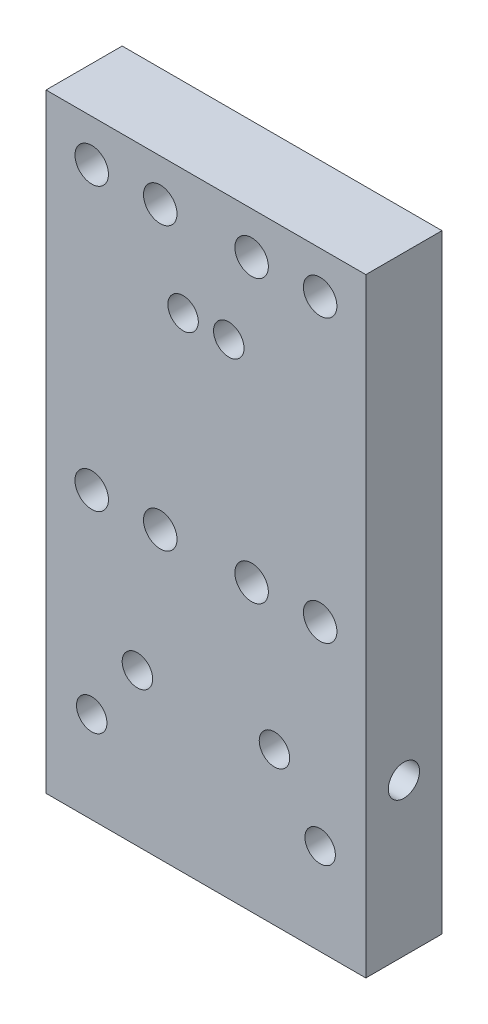
SolidWorks part; units mm, degrees
material "Ceramic Porcelain"
ref_plane "Front Plane" through (0, 0, 0) normal (0, 0, 1) x (1, 0, 0)
ref_plane "Top Plane" through (0, 0, 0) normal (0, 1, 0) x (1, 0, 0)
ref_plane "Right Plane" through (0, 0, 0) normal (1, 0, 0) x (0, 0, -1)
sketch "Sketch1" plane through (0, 0, 0) normal (0, 1, 0) x (1, 0, 0)
  line L1 (-10.5, 2.5) -> (10.5, 2.5)
  line L2 (-10.5, 2.5) -> (-10.5, -2.5)
  line L3 (-10.5, -2.5) -> (10.5, -2.5)
  line L4 (10.5, 2.5) -> (10.5, -2.5)
  point P4 (0, 2.5)
  point P6 (10.5, 0)
  dimension "D1" = 21
  dimension "D2" = 5
extrude "Boss-Extrude1" add sketch "Sketch1" along normal blind 40
hole_wizard "M2.5 Tapped Hole1" positions "Sketch4" profile "Sketch5" tap size "M2.5" standard "ISO"
sketch "Sketch4" plane through (0, 0, 0) normal (0, -1, 0) x (-1, 0, 0)
  line L0 (-10.5, 2.5) -> (10.5, 2.5) construction
  line L1 (-10.5, -2.5) -> (-10.5, 2.5) construction
  line L2 (-10.5, 2.5) -> (10.5, 2.5)
  line L3 (-10.5, -2.5) -> (-10.5, 2.5)
  line L4 (10.5, 2.5) -> (10.5, -2.5) construction
  point P0 (7.5, 0)
  point P2 (-7.5, 0)
  point P9 (-10.5, 0)
  dimension "D1" = 3
  dimension "D2" = 3
cosmetic thread "Hole Thread1" parameters "D1"=5, "D2"=2.5
cosmetic thread "Hole Thread2" parameters "D1"=5, "D2"=2.5
sketch "Sketch5" plane through (-7.5, 0, 0) normal (1, 0, 0) x (0, 0, -1)
  line L0 (0, 0) -> (0, 10.6159)
  line L1 (0, 10.6159) -> (1.025, 10)
  line L2 (1.025, 10) -> (1.025, 0)
  line L5 (1.025, 0) -> (0, 0)
  line L10 (0, 10.6159) -> (-1.025, 10) construction
  line L11 (0, -6.35) -> (0, 107.95) construction
  dimension "Tap Drill Dia." = 2.05
  dimension "Tap Drill Depth" = 10
  dimension "Drill Angle" = 118
hole_wizard "M2 Clearance Hole1" positions "Sketch6" profile "Sketch7" hole size "M2" standard "ISO" end condition through all
sketch "Sketch6" plane through (0, 0, -2.5) normal (0, 0, -1) x (-1, 0, 0)
  line L0 (10.5, 40) -> (10.5, 0) construction
  line L1 (-10.5, 40) -> (-10.5, 0) construction
  line L2 (-10.5, 40) -> (10.5, 40) construction
  line L3 (10.5, 40) -> (10.5, 0)
  line L4 (-10.5, 40) -> (-10.5, 0)
  line L5 (-10.5, 40) -> (10.5, 40)
  line L11 (-10.5, 17) -> (10.5, 17)
  line L13 (-10.5, 35.5) -> (10.5, 35.5)
  point P0 (-7.5, 37.25)
  point P2 (7.5, 37.25)
  point P4 (-7.5, 18.75)
  point P6 (7.5, 18.75)
  point P30 (-3, 37.25)
  point P32 (3, 37.25)
  point P35 (-3, 18.75)
  point P37 (3, 18.75)
  dimension "D1" = 3
  dimension "D2" = 3
  dimension "D3" = 4.5
  dimension "D4" = 23
  dimension "D5" = 1.75
  dimension "D6" = 1.75
  dimension "D7" = 4.5
  dimension "D8" = 4.5
sketch "Sketch7" plane through (7.5, 37.25, -2.5) normal (1, 0, 0) x (0, 1, 0)
  line L0 (0, 0) -> (0, 5)
  line L1 (0, 5) -> (1.1, 5)
  line L2 (1.1, 5) -> (1.1, 0)
  line L5 (1.1, 0) -> (0, 0)
  line L11 (0, -6.35) -> (0, 107.95) construction
  dimension "Thru Hole Dia." = 2.2
  dimension "Thru Hole Depth" = 5
hole_wizard "Ø2.0 (2) Diameter Hole2" positions "Sketch8" profile "Sketch9" hole size "Ø2.0" standard "ISO" end condition through all
sketch "Sketch8" plane through (0, 0, -2.5) normal (0, 0, -1) x (-1, 0, 0)
  line L9 (-1.5, 31.81) -> (1.5, 31.81)
  line L12 (0, 40) -> (0, 0)
  line L13 (-10.5, 40) -> (10.5, 40) construction
  line L14 (-10.5, 0) -> (10.5, 0) construction
  point P0 (1.5, 31.81)
  point P16 (-1.5, 31.81)
  point P54 (0, 31.81)
  dimension "D1" = 3
  dimension "D2" = 31.81
sketch "Sketch9" plane through (-1.5, 31.81, -2.5) normal (1, 0, 0) x (0, 1, 0)
  line L0 (0, 0) -> (0, 5)
  line L1 (0, 5) -> (1, 5)
  line L2 (1, 5) -> (1, 0)
  line L5 (1, 0) -> (0, 0)
  line L11 (0, -6.35) -> (0, 107.95) construction
  dimension "Thru Hole Dia." = 2
  dimension "Thru Hole Depth" = 5
hole_wizard "M2.5 Tapped Hole2" positions "Sketch10" profile "Sketch11" tap size "M2.5" standard "ISO"
sketch "Sketch10" plane through (10.5, 0, 0) normal (1, 0, 0) x (0, 0, -1)
  line L0 (-2.5, 0) -> (2.5, 0) construction
  line L1 (-2.5, 0) -> (2.5, 0)
  point P0 (0, 10)
  point P5 (0, 0)
  dimension "D1" = 10
cosmetic thread "Hole Thread3" parameters "D1"=5, "D2"=2.5
sketch "Sketch11" plane through (10.5, 10, 0) normal (0, 1, 0) x (0, 0, -1)
  line L0 (0, 0) -> (0, 6.9659)
  line L1 (0, 6.9659) -> (1.025, 6.35)
  line L2 (1.025, 6.35) -> (1.025, 0)
  line L5 (1.025, 0) -> (0, 0)
  line L10 (0, 6.9659) -> (-1.025, 6.35) construction
  line L11 (0, -6.35) -> (0, 107.95) construction
  dimension "Tap Drill Dia." = 2.05
  dimension "Tap Drill Depth" = 6.35
  dimension "Drill Angle" = 118
sketch "Sketch13" plane through (0, 0, -2.5) normal (0, 0, -1) x (-1, 0, 0)
  line L0 (-10.5, 40) -> (-10.5, 0) construction
  line L1 (-10.5, 21.75) -> (10.5, 21.75)
  line L2 (-10.5, 21.75) -> (-10.5, 15.75)
  line L3 (-10.5, 15.75) -> (10.5, 15.75)
  line L4 (10.5, 21.75) -> (10.5, 15.75)
  line L5 (10.5, 40) -> (10.5, 0) construction
  line L7 (-10.5, 40) -> (10.5, 40)
  line L8 (-10.5, 40) -> (-10.5, 34.25)
  line L9 (-10.5, 34.25) -> (10.5, 34.25)
  line L10 (10.5, 40) -> (10.5, 34.25)
  circle A0 centre (-7.5, 37.25) radius 1.1 construction
  circle A1 centre (-7.5, 18.75) radius 1.1 construction
  dimension "D1" = 3
  dimension "D2" = 3
  dimension "D3" = 6
extrude "Cut-Extrude2" [suppressed] cut sketch "Sketch13" against normal blind 3
mirror "Mirror1" about plane through (0, 0, 0) normal (1, 0, 0) of "M2.5 Tapped Hole2"
hole_wizard "Ø2.0 (2) Diameter Hole3" positions "Sketch14" profile "Sketch15" hole size "Ø2.0" standard "ISO" end condition through all
sketch "Sketch14" plane through (0, 0, -2.5) normal (0, 0, -1) x (-1, 0, 0)
  line L0 (-10.5, 40) -> (-10.5, 0) construction
  line L1 (10.5, 40) -> (10.5, 0) construction
  line L2 (-10.5, 0) -> (10.5, 0) construction
  point P0 (-4.5, 10)
  point P2 (4.5, 10)
  point P9 (-7.5, 6)
  point P11 (7.5, 6)
  dimension "D1" = 6
  dimension "D2" = 6
  dimension "D3" = 10
  dimension "D4" = 3
  dimension "D5" = 3
  dimension "D6" = 6
sketch "Sketch15" plane through (4.5, 10, -2.5) normal (1, 0, 0) x (0, 1, 0)
  line L0 (0, 0) -> (0, 5)
  line L1 (0, 5) -> (1, 5)
  line L2 (1, 5) -> (1, 0)
  line L5 (1, 0) -> (0, 0)
  line L11 (0, -6.35) -> (0, 107.95) construction
  dimension "Thru Hole Dia." = 2
  dimension "Thru Hole Depth" = 5
